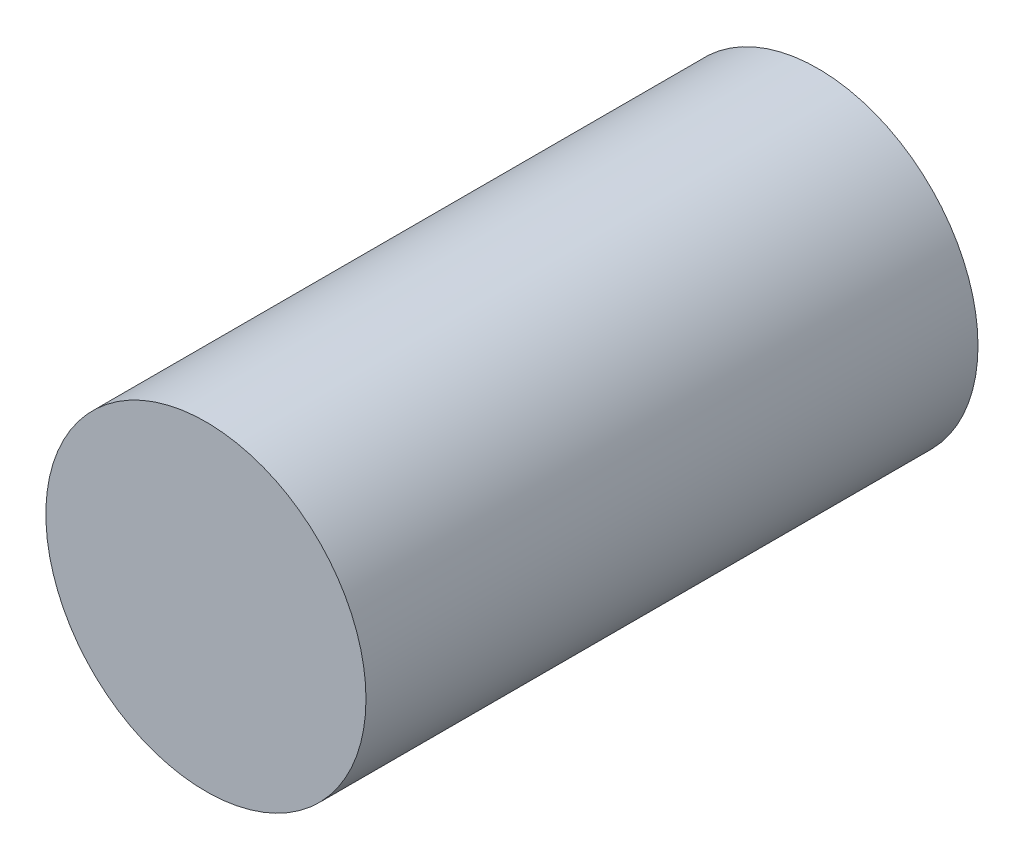
SolidWorks part; units mm, degrees
ref_plane "Front Plane" through (0, 0, 0) normal (0, 0, 1) x (1, 0, 0)
ref_plane "Top Plane" through (0, 0, 0) normal (0, 1, 0) x (1, 0, 0)
ref_plane "Right Plane" through (0, 0, 0) normal (1, 0, 0) x (0, 0, -1)
sketch "Sketch1" plane through (0, 0, 0) normal (0, 0, 1) x (1, 0, 0)
  line L0 (0, 0) -> (0, 17) construction
  line L1 (0, 0) -> (14.7224, -8.5) construction
  line L2 (0, 0) -> (-14.7224, -8.5) construction
  circle A0 centre (0, 0) radius 17
  dimension "D1" = 120
  dimension "D3" = 34
  dimension "D2" = 120
extrude "Boss-Extrude1" add sketch "Sketch1" along normal blind 65
